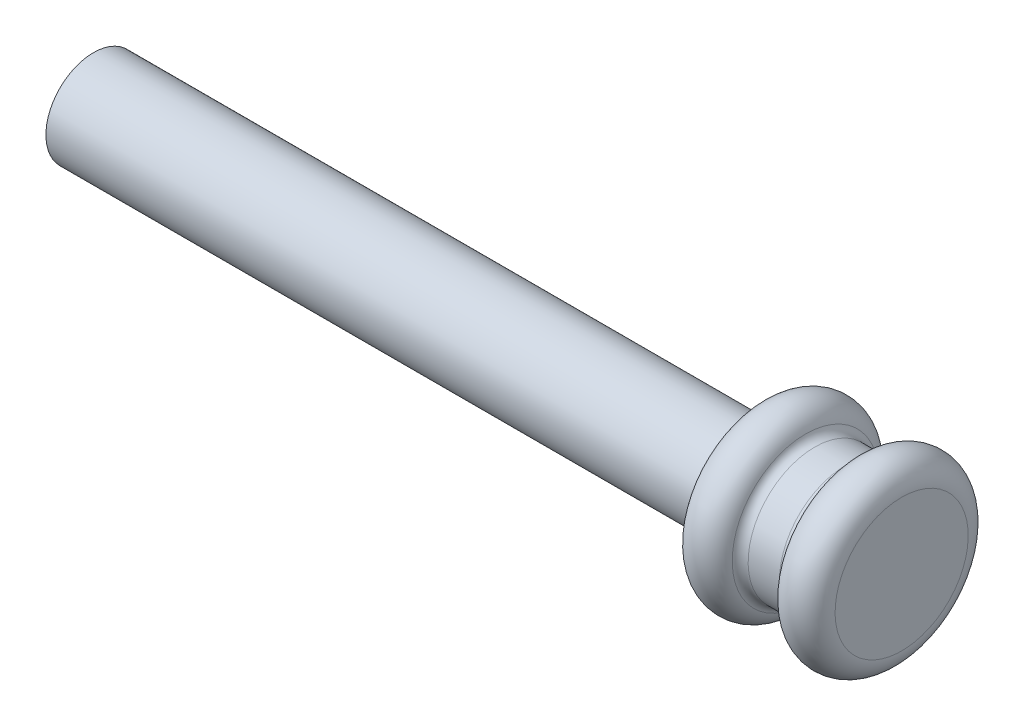
SolidWorks part; units mm, degrees
ref_plane "Front Plane" through (0, 0, 0) normal (0, 0, 1) x (1, 0, 0)
ref_plane "Top Plane" through (0, 0, 0) normal (0, 1, 0) x (1, 0, 0)
ref_plane "Right Plane" through (0, 0, 0) normal (1, 0, 0) x (0, 0, -1)
sketch "Sketch1" plane through (0, 0, 0) normal (0, 0, 1) x (1, 0, 0)
  line L0 (-2.7396, 0) -> (0.5521, 0)
  line L3 (-2.7396, 0) -> (0.5521, 0)
  line L4 (-1.0937, -7) -> (11.0356, -7) construction
  line L5 (11.0356, -7) -> (-11.759, -7) construction
  line L6 (-8.5937, 0) -> (-8.5937, -2)
  line L7 (-8.5937, -2) -> (6.4063, -2)
  line L8 (6.4063, -2) -> (6.4063, 0)
  line L9 (0, -10.45) -> (0, 10.45) construction
  arc A0 (-3.698, 0.7143) -> (-8.5937, 0) centre (-6.0937, 0) ccw
  arc A1 (6.4063, 0) -> (1.5105, 0.7143) centre (3.9063, 0) ccw
  arc A2 (-2.7396, 0) -> (-3.698, 0.7143) centre (-2.7396, 1) cw
  arc A3 (1.5105, 0.7143) -> (0.5521, 0) centre (0.5521, 1) cw
  point P13 (-1.0937, 0)
  dimension "D1" = 5
  dimension "D2" = 5
  dimension "D4" = 1
  dimension "D5" = 1
  dimension "D3" = 10
  dimension "D6" = 7
  dimension "D7" = 2
revolve "Revolve2" add sketch "Sketch1" angle 360 about L5
ref_plane "Plane1" through (6.4063, 0, 0) normal (1, 0, 0) x (0, 0, -1)
sketch "Sketch2" plane through (6.4063, 0, 0) normal (1, 0, 0) x (0, 0, -1)
  circle A0 centre (0, -7) radius 5
extrude "Boss-Extrude1" add sketch "Sketch2" along a picked direction on the side against the normal blind 85
